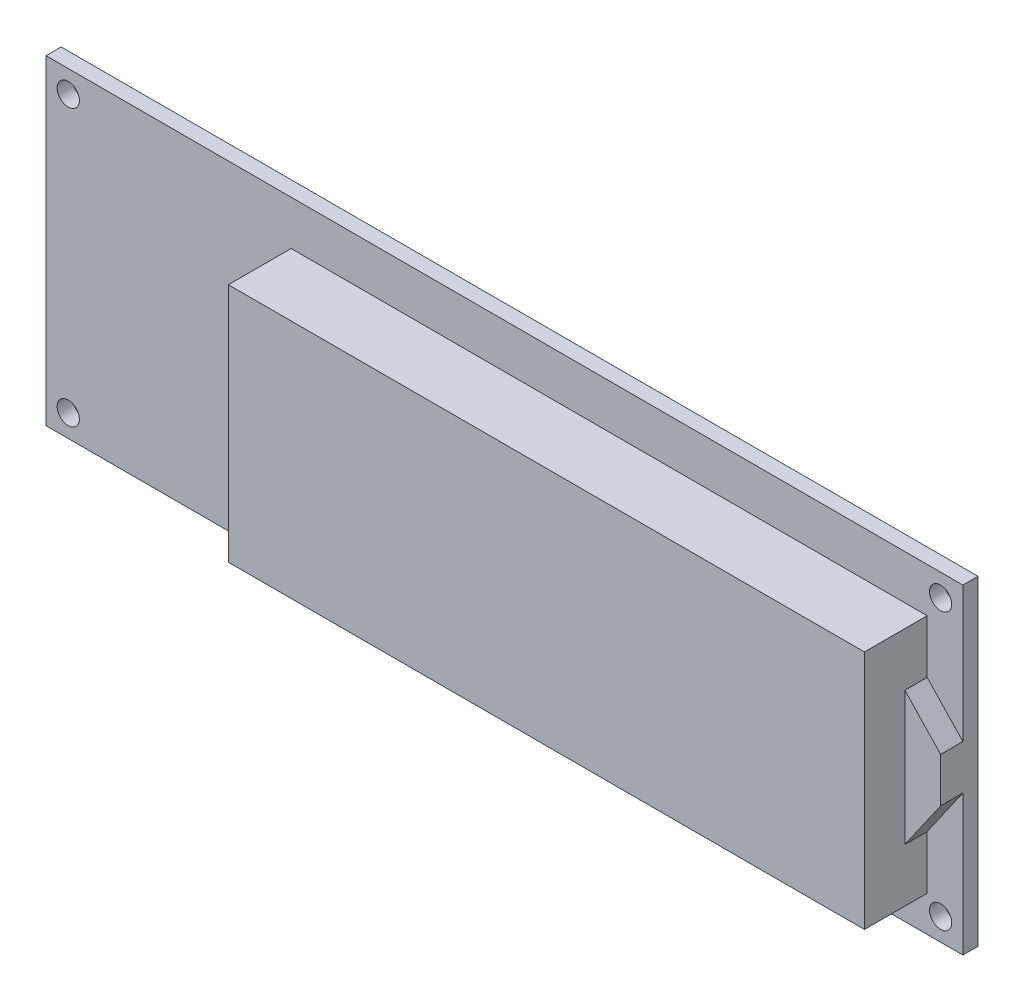
SolidWorks part; units mm, degrees
material "PA tipo 6"
ref_plane "Alzado" through (0, 0, 0) normal (0, 0, 1) x (1, 0, 0)
ref_plane "Planta" through (0, 0, 0) normal (0, 1, 0) x (1, 0, 0)
ref_plane "Vista lateral" through (0, 0, 0) normal (1, 0, 0) x (0, 0, -1)
sketch "Croquis1" plane through (0, 0, 0) normal (0, 0, 1) x (1, 0, 0)
  line L1 (-51.5, 18) -> (51.5, 18)
  line L2 (-51.5, 18) -> (-51.5, -18)
  line L3 (-51.5, -18) -> (51.5, -18)
  line L4 (51.5, 18) -> (51.5, -18)
  line L5 (-51.5, 18) -> (51.5, -18) construction
  line L6 (-51.5, -18) -> (51.5, 18) construction
  point P0 (0, 0)
  dimension "D1" = 103
  dimension "D2" = 36
extrude "Saliente-Extruir1" add sketch "Croquis1" along normal blind 1.7
sketch "Croquis2" plane through (0, 0, 1.7) normal (0, 0, 1) x (1, 0, 0)
  line L0 (-51.5, -18) -> (51.5, -18) construction
  line L1 (-23.96, 13.01) -> (47.49, 13.01)
  line L2 (-23.96, 13.01) -> (-23.96, -13.99)
  line L3 (-23.96, -13.99) -> (47.49, -13.99)
  line L4 (47.49, 13.01) -> (47.49, -13.99)
  line L5 (-23.96, 13.01) -> (47.49, -13.99) construction
  line L6 (-23.96, -13.99) -> (47.49, 13.01) construction
  line L7 (51.5, -18) -> (51.5, 18) construction
  point P0 (11.765, -0.49)
  dimension "D1" = 71.45
  dimension "D2" = 27
  dimension "D3" = 4.01
  dimension "D4" = 4.01
extrude "Saliente-Extruir2" add sketch "Croquis2" along normal blind 7.05
sketch "Croquis3" plane through (0, 0, 1.7) normal (0, 0, 1) x (1, 0, 0)
  line L0 (-51.5, 18) -> (-51.5, -18) construction
  line L1 (51.5, 18) -> (-51.5, 18) construction
  line L2 (-51.5, -18) -> (51.5, -18) construction
  line L3 (51.5, -18) -> (51.5, 18) construction
  circle A0 centre (-49, 15.5) radius 1.25
  circle A1 centre (-49, -15.5) radius 1.25
  circle A2 centre (49, 15.5) radius 1.25
  circle A3 centre (49, -15.5) radius 1.25
  dimension "D1" = 2.5
  dimension "D4" = 2.5
  dimension "D7" = 2.5
  dimension "D10" = 2.5
  dimension "D2" = 2.5
  dimension "D3" = 2.5
  dimension "D5" = 2.5
  dimension "D6" = 2.5
  dimension "D8" = 2.5
  dimension "D9" = 2.5
  dimension "D11" = 2.5
  dimension "D12" = 2.5
extrude "Cortar-Extruir1" cut sketch "Croquis3" against normal blind 6
sketch "Croquis4" plane through (0, 0, 1.7) normal (0, 0, 1) x (1, 0, 0)
  line L0 (47.49, 7.01) -> (51.5, 2.7758)
  line L1 (47.49, -13.99) -> (47.49, 13.01) construction
  line L2 (51.5, -18) -> (51.5, 18) construction
  line L3 (47.49, -7.99) -> (51.5, -2.2342)
  line L4 (47.49, -7.99) -> (47.49, 7.01)
  line L5 (51.5, -2.2342) -> (51.5, 2.7758)
  line L6 (47.49, -0.49) -> (51.5, -0.49) construction
  dimension "D1" = 5.01
  dimension "D2" = 15
  dimension "D3" = 7.5
  dimension "D4" = 5.8317
extrude "Saliente-Extruir3" add sketch "Croquis4" along normal blind 2.5
